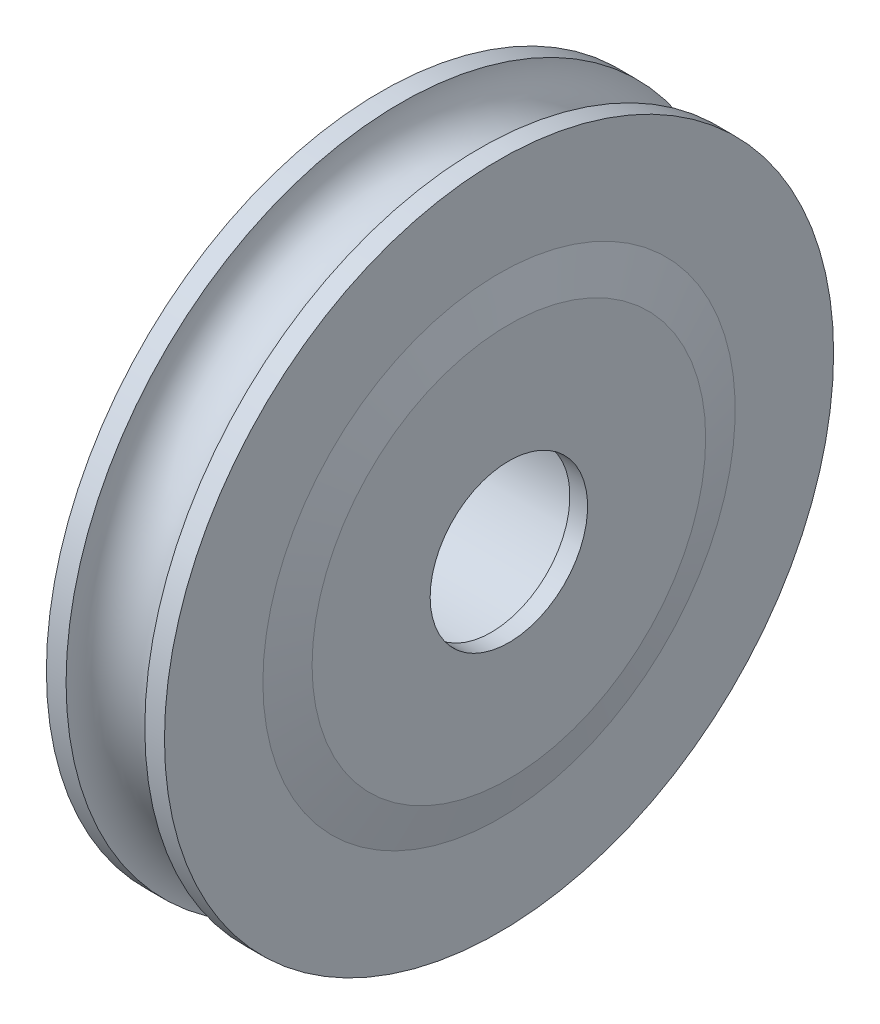
SolidWorks part; units mm, degrees
ref_plane "前视基准面" through (0, 0, 0) normal (0, 0, 1) x (1, 0, 0)
ref_plane "上视基准面" through (0, 0, 0) normal (0, 1, 0) x (1, 0, 0)
ref_plane "右视基准面" through (0, 0, 0) normal (1, 0, 0) x (0, 0, -1)
sketch "草图1" plane through (0, 0, 0) normal (0, 0, 1) x (1, 0, 0)
  line L0 (5.6, 5.1) -> (5.6, 4)
  line L1 (6.5, 10) -> (6.5, 4)
  line L2 (5.6, 4) -> (6.5, 4)
  line L3 (0, 17) -> (1, 17)
  line L4 (6, 12) -> (6.5, 10)
  line L5 (5, 17) -> (6, 17)
  line L6 (6, 17) -> (6, 12)
  line L7 (0, 0) -> (9.4205, 0) construction
  line L8 (5.6, 5.1) -> (0, 5.1)
  line L9 (0, 17) -> (0, 5.1)
  arc A0 (1, 17) -> (5, 17) centre (3, 16.9902) ccw
  dimension "D2" = 6
  dimension "D8" = 2
  dimension "D9" = 5
  dimension "D12" = 4
  dimension "D7" = 6
  dimension "D5" = 2
  dimension "D1" = 5.6
  dimension "D3" = 17
  dimension "D4" = 5.1
  dimension "D6" = 6.5
  dimension "D10" = 1
  dimension "D11" = 1
revolve "旋转1" add sketch "草图1" angle 360 about L7
